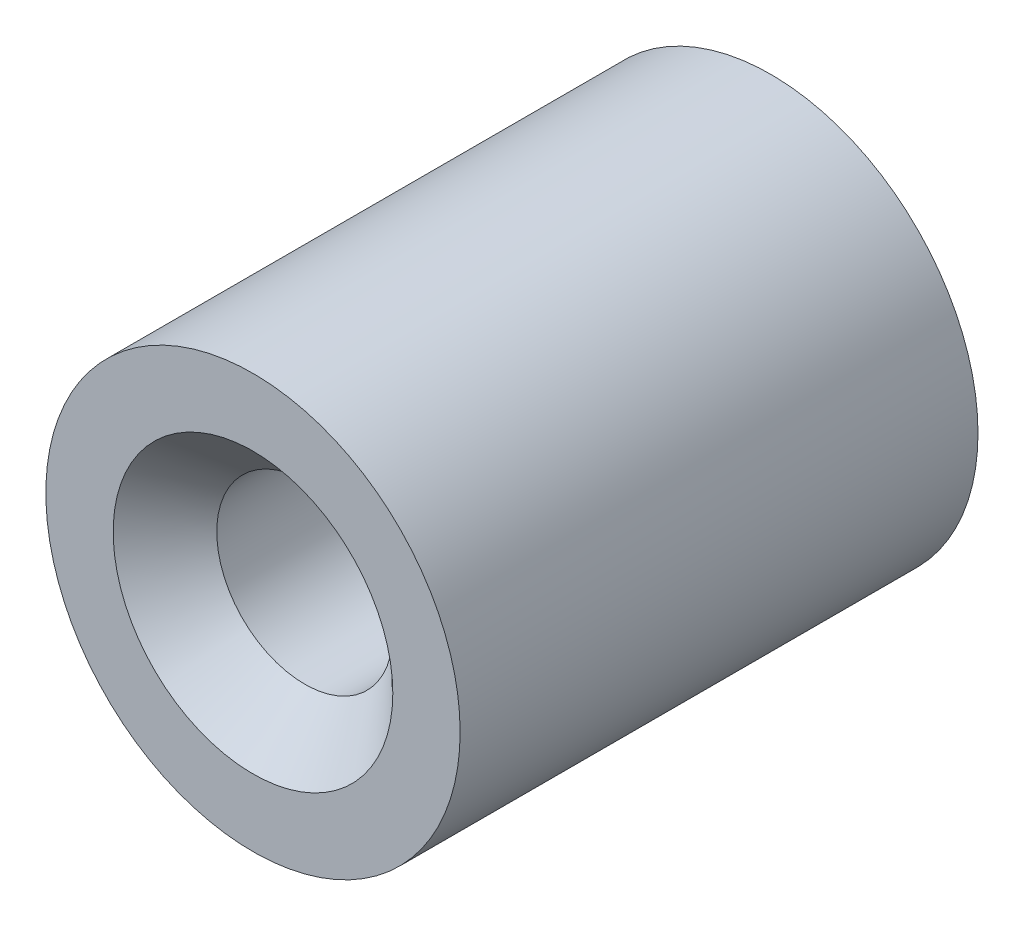
SolidWorks part; units mm, degrees
material "AISI 1020"
ref_plane "Спереди" through (0, 0, 0) normal (0, 0, 1) x (1, 0, 0)
ref_plane "Сверху" through (0, 0, 0) normal (0, 1, 0) x (1, 0, 0)
ref_plane "Справа" through (0, 0, 0) normal (1, 0, 0) x (0, 0, -1)
sketch "Эскиз1" plane through (0, 0, 0) normal (0, 0, 1) x (1, 0, 0)
  circle A0 centre (0, 0) radius 8
  dimension "D1" = 16
extrude "Бобышка-Вытянуть1" add sketch "Эскиз1" along normal blind 20
hole_wizard "Отверстие обработанное метчиком M81" positions "Эскиз2" profile "Эскиз3" tap size "M8" standard "ISO" end condition through all
sketch "Эскиз2" plane through (0, 0, 20) normal (0, 0, 1) x (1, 0, 0)
  point P0 (0, 0)
sketch "Эскиз3" plane through (0, 0, 20) normal (1, 0, 0) x (0, -1, 0)
  line L0 (0, 0) -> (0, 20)
  line L1 (0, 20) -> (3.4, 20)
  line L2 (3.4, 20) -> (3.4, 0)
  line L5 (3.4, 0) -> (0, 0)
  line L11 (0, -6.35) -> (0, 107.95) construction
  dimension "Диаметр проходного сверла" = 6.8
  dimension "Глубина проходного сверла" = 20
cosmetic thread "Отверстие резьбы1" parameters "D2"=8
chamfer "Фаска1" distance 2 angle 45 1 edges at (3.4, 0, 20)
